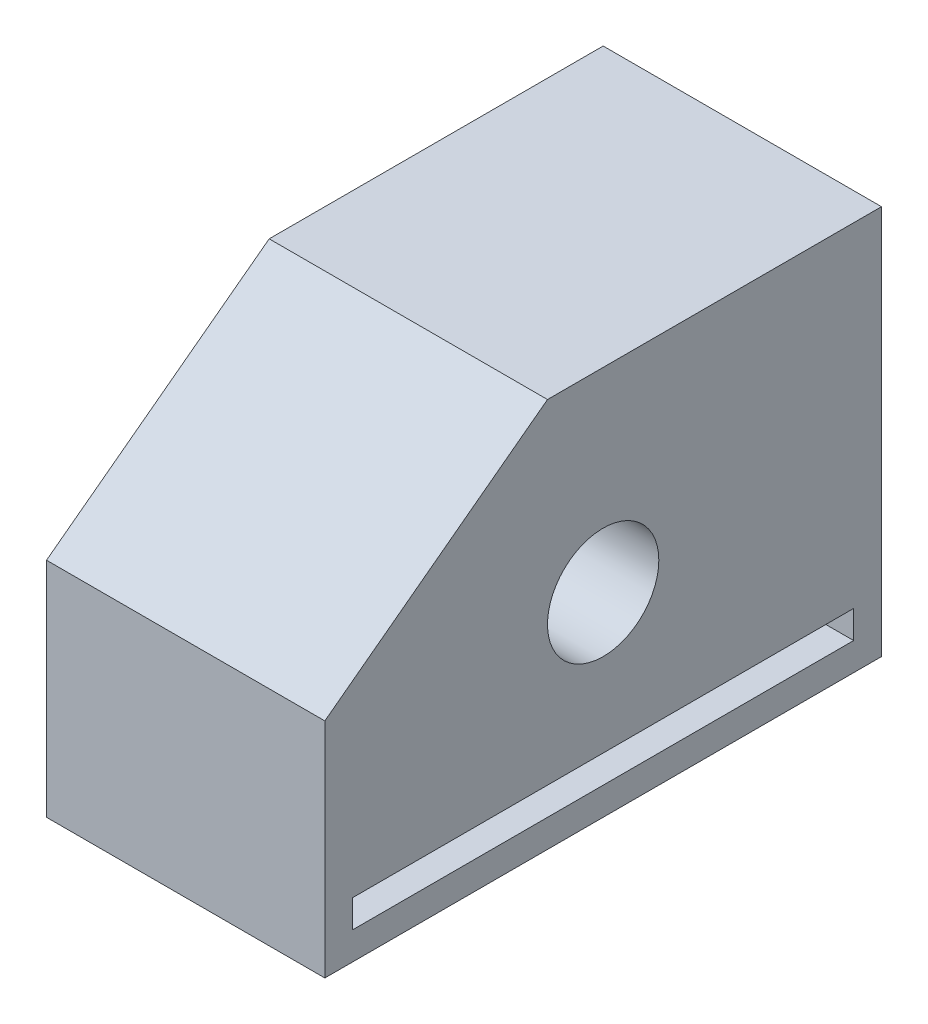
SolidWorks part; units mm, degrees
ref_plane "Front Plane" through (0, 0, 0) normal (0, 0, 1) x (1, 0, 0)
ref_plane "Top Plane" through (0, 0, 0) normal (0, 1, 0) x (1, 0, 0)
ref_plane "Right Plane" through (0, 0, 0) normal (1, 0, 0) x (0, 0, -1)
sketch "Sketch1" plane through (0, 0, 0) normal (1, 0, 0) x (0, 0, -1)
  line L0 (0, 40) -> (40, 70)
  line L1 (0, 0) -> (100, 0)
  line L2 (0, 0) -> (0, 70)
  line L3 (0, 70) -> (100, 70)
  line L4 (100, 0) -> (100, 70)
  point P7 (32.9069, 70)
  point P8 (41.2092, 70)
  point P9 (0, 0)
  point P10 (40.2325, 70)
  dimension "D1" = 100
  dimension "D2" = 70
  dimension "D3" = 50
  dimension "D4" = 40
extrude "Boss-Extrude1" add sketch "Sketch1" along normal blind 50 contours L1 L4 L3 L0 L2
sketch "Sketch2" plane through (50, 0, 0) normal (1, 0, 0) x (0, 0, -1)
  line L0 (0, 0) -> (100, 70) construction
  circle A0 centre (50, 35) radius 10
  point P6 (0, 0)
  dimension "D1" = 20
extrude "Cut-Extrude1" cut sketch "Sketch2" against normal through all
sketch "Sketch3" plane through (50, 0, 0) normal (1, 0, 0) x (0, 0, -1)
  line L0 (0, 0) -> (100, 0) construction
  line L1 (5, 5) -> (95, 5)
  line L2 (5, 5) -> (5, 10)
  line L3 (5, 10) -> (95, 10)
  line L4 (95, 5) -> (95, 10)
  line L5 (100, 0) -> (100, 70) construction
  line L6 (0, 0) -> (0, 40) construction
  dimension "D1" = 5
  dimension "D2" = 5
  dimension "D3" = 5
  dimension "D4" = 5
extrude "Cut-Extrude2" cut sketch "Sketch3" against normal through all
